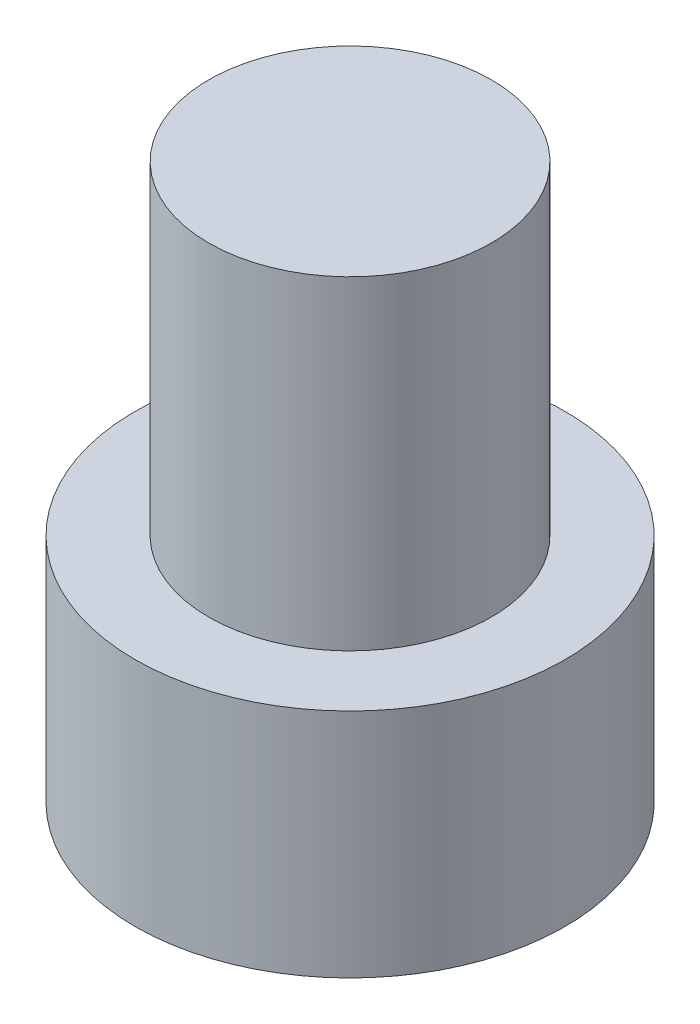
SolidWorks part; units mm, degrees
ref_plane "Front Plane" through (0, 0, 0) normal (0, 0, 1) x (1, 0, 0)
ref_plane "Top Plane" through (0, 0, 0) normal (0, 1, 0) x (1, 0, 0)
ref_plane "Right Plane" through (0, 0, 0) normal (1, 0, 0) x (0, 0, -1)
sketch "Sketch1" plane through (0, 0, 0) normal (0, 1, 0) x (1, 0, 0)
  circle A0 centre (0, 0) radius 7.3
  dimension "D1" = 14.6
extrude "Boss-Extrude1" add sketch "Sketch1" along normal blind 7.85
sketch "Sketch2" plane through (0, 7.85, 0) normal (0, 1, 0) x (1, 0, 0)
  circle A0 centre (0, 0) radius 4.8
  dimension "D1" = 9.6
extrude "Boss-Extrude2" add sketch "Sketch2" along normal blind 11
